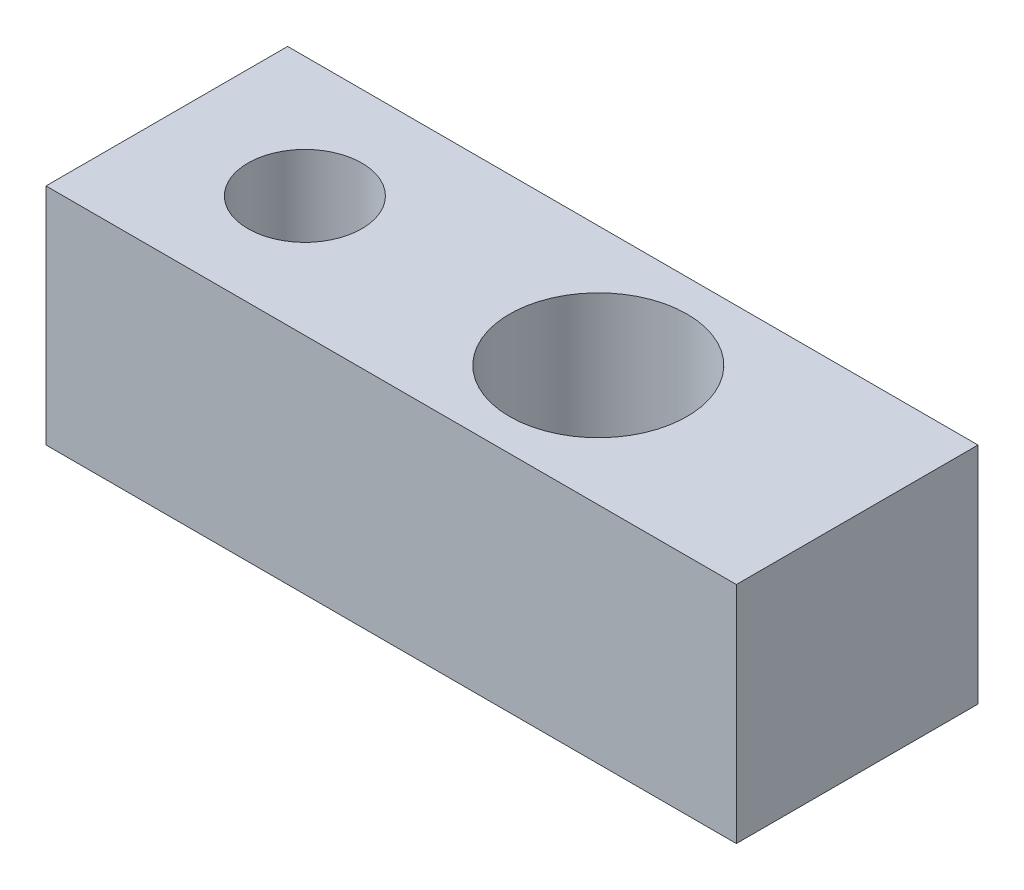
SolidWorks part; units mm, degrees
ref_plane "Front Plane" through (0, 0, 0) normal (0, 0, 1) x (1, 0, 0)
ref_plane "Top Plane" through (0, 0, 0) normal (0, 1, 0) x (1, 0, 0)
ref_plane "Right Plane" through (0, 0, 0) normal (1, 0, 0) x (0, 0, -1)
sketch "Sketch1" plane through (0, 0, 0) normal (0, 1, 0) x (1, 0, 0)
  line L5 (-4, 3.5) -> (16, 3.5)
  line L6 (-4, 3.5) -> (-4, -3.5)
  line L7 (-4, -3.5) -> (16, -3.5)
  line L8 (16, 3.5) -> (16, -3.5)
  line L9 (-4, 3.5) -> (16, -3.5) construction
  line L10 (-4, -3.5) -> (16, 3.5) construction
  circle A1 centre (0, 0) radius 1.65
  circle A2 centre (8.5, 0) radius 2.5719
  point P3 (6, 0)
  point P13 (6.229, -1.0777)
  dimension "D1" = 20
  dimension "D2" = 7
  dimension "D3" = 3.3
  dimension "D4" = 0
  dimension "D5" = 4
  dimension "D6" = 8.5
  dimension "D7" = 0
extrude "Boss-Extrude1" add sketch "Sketch1" along normal blind 6.5
